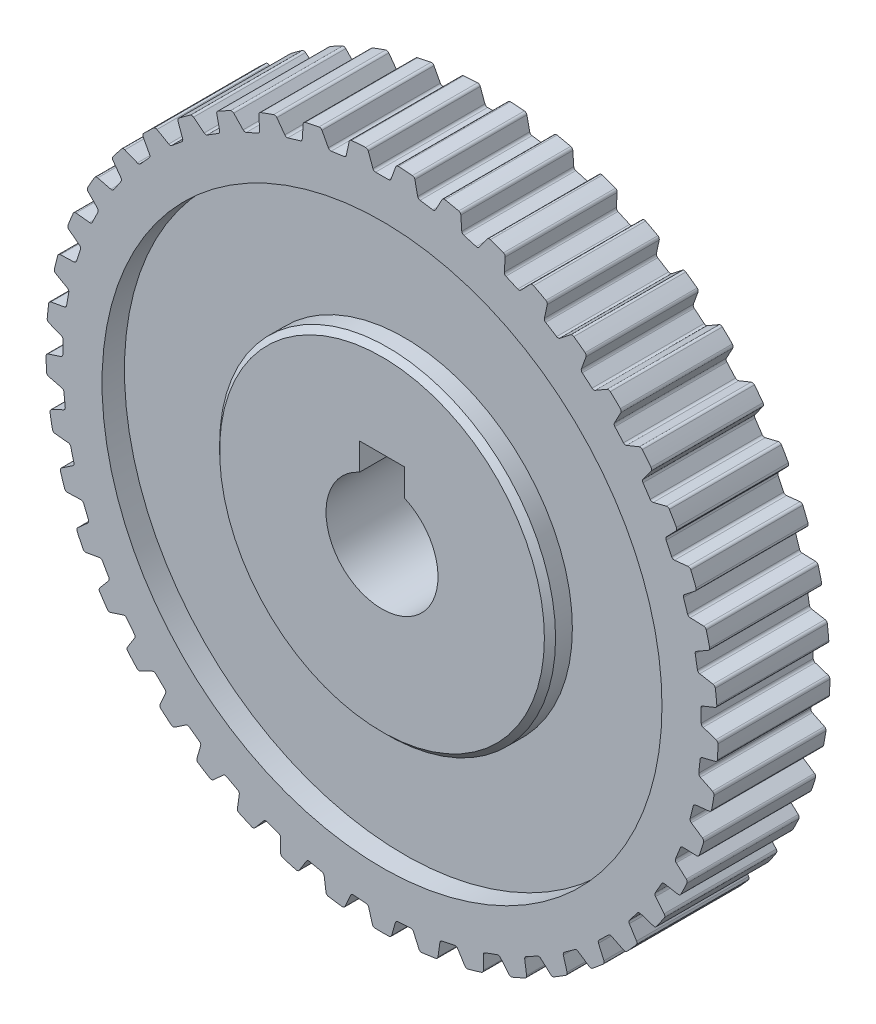
SolidWorks part; units mm, degrees
ref_plane "Front Plane" through (0, 0, 0) normal (0, 0, 1) x (1, 0, 0)
ref_plane "Top Plane" through (0, 0, 0) normal (0, 1, 0) x (1, 0, 0)
ref_plane "Right Plane" through (0, 0, 0) normal (1, 0, 0) x (0, 0, -1)
sketch "Sketch1" plane through (0, 0, 0) normal (0, 0, 1) x (1, 0, 0)
  line L0 (0, 0) -> (0, 58.5336) construction
  line L2 (-2, 7) -> (2, 7)
  line L3 (-2, 7) -> (-2, 4.5826)
  line L5 (2, 7) -> (2, 4.5826)
  line L6 (-2, 7) -> (0, 4.5447) construction
  line L7 (0, 4.5447) -> (2, 7) construction
  arc A0 (0.3603, 4.987) -> (-0.3603, 4.987) centre (0, 0) ccw
  circle A1 centre (0, 0) radius 30
  arc A2 (-2, 4.5826) -> (2, 4.5826) centre (0, 0) ccw
  point P4 (0, 4.5447)
  dimension "D1" = 60
  dimension "D2" = 10
  dimension "D3" = 4
  dimension "D4" = 7
  dimension "D5" = 0.3603
extrude "Boss-Extrude1" add sketch "Sketch1" along normal blind 10 contours A1 A2 L3 L2 L5
sketch "Sketch2" plane through (0, 0, 10) normal (0, 0, 1) x (1, 0, 0)
  line L0 (0, 0) -> (0, 40.4793) construction
  line L1 (-0.75, 28.5) -> (0.75, 28.5)
  line L2 (0.75, 28.5) -> (1.2859, 29.9724)
  line L3 (-0.75, 28.5) -> (-1.2859, 29.9724)
  circle A0 centre (0, 0) radius 30 construction
  circle A1 centre (0, 0) radius 30
  point P6 (0, 0)
  circle M10 centre (0, 0) radius 30
  dimension "D1" = 20
  dimension "D2" = 20
  dimension "D3" = 1.5
  dimension "D4" = 28.5
extrude "Cut-Extrude1" cut sketch "Sketch2" against normal through all contours L1 L0 A1 L3 | L0 L1 L2 M10
pattern_circular "CirPattern1" count 45 over 360 about axis through (0, 0, 0) along (0, 0, 1) of "Cut-Extrude1"
sketch "Sketch3" plane through (0, 0, 10) normal (0, 0, 1) x (1, 0, 0)
  circle A0 centre (0, 0) radius 25
  dimension "D1" = 50
extrude "Cut-Extrude-Thin1" cut sketch "Sketch3" against normal blind 2 thin thin type one direction reverse wall 10
chamfer "Chamfer1" distance 0.5 angle 45 1 edges at (15, 0, 10)
ref_plane "Plane1" through (0, 0, 5) normal (0, 0, 1) x (1, 0, 0)
mirror "Mirror2" about plane through (0, 0, 5) normal (0, 0, 1) of "Cut-Extrude-Thin1"
chamfer "Chamfer2" distance 0.5 angle 45 1 edges at (15, 0, 0)
fillet "Fillet1" radius 0.25 110 edges at (29.999, -0.2391, 5) (28.5088, 0.2451, 5) (28.4565, 1.7442, 5) (29.7404, 3.9383, 5) (27.9368, 5.6876, 5) (28.1081, 10.485, 5) (27.5027, 11.9833, 5) (25.9444, 11.8195, 5) (25.5673, 15.6943, 5) (24.047, 15.3152, 5) (23.1343, 19.0998, 5) (20.251, 22.1336, 5) (18.894, 21.3502, 5) (17.7449, 22.3144, 5) (18.2808, 23.7868, 5) (16.9735, 24.7366, 5) (14.4667, 24.5668, 5) (14.7924, 26.0995, 5) (12.2772, 25.731, 5) (8.5766, 27.1892, 5) (7.1347, 27.6027, 5) (5.4448, 29.5018, 5) (2.898, 29.8597, 5) (1.2859, 29.9724, 5) (0.75, 28.5, 5) (-1.2859, 29.9724, 5) (-2.898, 29.8597, 5) (-4.7091, 28.1183, 5) (-7.1347, 27.6027, 5) (-8.5766, 27.1892, 5) (-9.4976, 28.4569, 5) (-13.3656, 26.8581, 5) (-14.7924, 26.0995, 5) (-14.4667, 24.5668, 5) (-15.7387, 23.7719, 5) (-16.9735, 24.7366, 5) (-18.2808, 23.7868, 5) (-17.7449, 22.3144, 5) (-21.4134, 21.0111, 5) (-21.6815, 18.5129, 5) (-23.1343, 19.0998, 5) (-24.1292, 17.8264, 5) (-23.2082, 16.5588, 5) (-25.5673, 15.6943, 5) (-26.3753, 14.2948, 5) (-27.5027, 11.9833, 5) (-28.1081, 10.485, 5) (-26.8733, 9.5203, 5) (-27.3369, 8.0937, 5) (-29.2938, 6.471, 5) (-28.1973, 4.2104, 5) (-29.9093, 2.3312, 5) (-28.4565, 1.7442, 5) (-29.999, -0.2391, 5) (-29.9427, -1.8541, 5) (-29.6738, -4.4118, 5) (-27.8349, -6.1671, 5) (-27.472, -7.6225, 5) (-28.771, -8.4987, 5) (-26.7057, -9.9809, 5) (-26.5998, -13.8726, 5) (-25.0567, -13.6005, 5) (-24.3067, -14.8995, 5) (-25.3139, -16.0999, 5) (-22.9201, -16.9553, 5) (-21.9966, -18.1374, 5) (-21.7456, -20.6671, 5) (-19.8956, -22.4536, 5) (-18.6577, -23.4924, 5) (-17.3586, -22.6161, 5) (-16.577, -25.004, 5) (-15.2066, -25.8604, 5) (-14.0422, -24.8119, 5) (-12.7177, -25.5161, 5) (-11.4595, -27.7251, 5) (-10.4523, -26.5247, 5) (-9.0428, -28.6047, 5) (-6.6591, -27.7213, 5) (-5.1919, -28.0331, 5) (-4.9738, -29.5848, 5) (-3.3736, -29.8097, 5) (-2.7362, -28.3783, 5) (-1.2399, -28.4829, 5) (-0.808, -29.9891, 5) (0.808, -29.9891, 5) (1.2399, -28.4829, 5) (2.7362, -28.3783, 5) (4.9738, -29.5848, 5) (5.1919, -28.0331, 5) (7.4894, -29.0501, 5) (9.0428, -27.0378, 5) (11.4595, -27.7251, 5) (14.0422, -24.8119, 5) (15.2066, -25.8604, 5) (18.6577, -23.4924, 5) (19.2583, -21.0222, 5) (20.3373, -19.9802, 5) (21.7456, -20.6671, 5) (22.8269, -19.4662, 5) (21.9966, -18.1374, 5) (22.9201, -16.9553, 5) (25.0567, -13.6005, 5) (26.5998, -13.8726, 5) (27.3082, -12.4202, 5) (28.2717, -10.0356, 5) (28.771, -8.4987, 5) (27.8349, -6.1671, 5) (29.6738, -4.4118, 5) (28.2655, -3.725, 5) (28.4223, -2.2332, 5)
